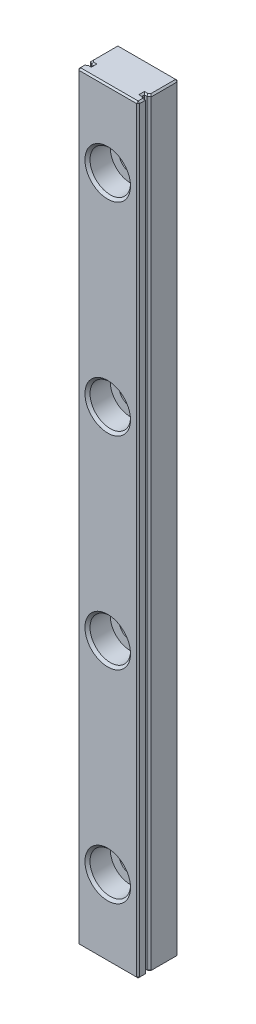
SolidWorks part; units mm, degrees
material "Простая углеродистая сталь"
ref_plane "Спереди" through (0, 0, 0) normal (0, 0, 1) x (1, 0, 0)
ref_plane "Сверху" through (0, 0, 0) normal (0, 1, 0) x (1, 0, 0)
ref_plane "Справа" through (0, 0, 0) normal (1, 0, 0) x (0, 0, -1)
sketch "Эскиз1" plane through (0, 0, 0) normal (0, 1, 0) x (1, 0, 0)
  line L0 (0, 0) -> (12, 0)
  line L1 (0, 0) -> (0, 8)
  line L2 (12, 0) -> (12, 8)
  line L3 (0, 8) -> (12, 8)
  dimension "D1" = 8
  dimension "D2" = 12
extrude "Бобышка-Вытянуть1" add sketch "Эскиз1" along normal blind 150
sketch "Эскиз2" plane through (0, 150, 0) normal (0, 1, 0) x (1, 0, 0)
  line L0 (12, 0) -> (12, 8) construction
  line L1 (11, 2.25) -> (11, 1.75)
  line L2 (11, 2.25) -> (11.5, 2.25)
  line L3 (11, 1.75) -> (11.5, 1.75)
  line L4 (12, 2.25) -> (12, 1.75) construction
  line L5 (11, 2) -> (12, 2) construction
  line L6 (0, 0) -> (12, 0) construction
  line L7 (12, 2) -> (11, 2) construction
  line L8 (11.5, 2.25) -> (11.5, 1.75) construction
  line L9 (12, 2.559) -> (12, 1.441)
  arc A0 (12, 2.559) -> (11.5, 2.25) centre (12, 2) ccw
  arc A1 (11.5, 1.75) -> (12, 1.441) centre (12, 2) ccw
  dimension "D4" = 0.5
  dimension "D1" = 0.5
  dimension "D2" = 1
  dimension "D3" = 2
extrude "Вырез-Вытянуть1" cut sketch "Эскиз2" against normal through all
sketch "Эскиз3" plane through (0, 150, 0) normal (0, 1, 0) x (1, 0, 0)
  line L0 (6, 0) -> (6, 8) construction
  line L1 (0, 0) -> (12, 0) construction
  line L2 (12, 8) -> (0, 8) construction
  line L3 (6, 4) -> (12, 4) construction
  line L4 (12, 2.559) -> (12, 8) construction
ref_plane "A" through (6, 0, 0) normal (1, 0, 0) x (0, 0, -1)
ref_plane "B" through (0, 0, -4) normal (0, 0, 1) x (1, 0, 0)
mirror "Зеркальное отражение1" about plane through (6, 0, 0) normal (1, 0, 0) of "Вырез-Вытянуть1"
sketch "Эскиз4" plane through (6, 0, 0) normal (1, 0, 0) x (0, 0, -1)
  line L0 (8, 135) -> (-11.3986, 135) construction
  line L1 (8, 150) -> (2.559, 150) construction
  line L2 (8, 150) -> (0, 150) construction
  line L3 (0, 150) -> (0, 133.1034) construction
  line L4 (0, 139) -> (4.5, 139)
  line L5 (4.5, 139) -> (4.5, 137.25)
  line L6 (4.5, 137.25) -> (8, 137.25)
  line L7 (8, 150) -> (8, 0) construction
  line L8 (8, 150) -> (8, 0) construction
  line L9 (0, 139) -> (0, 135)
  line L10 (8, 137.25) -> (8, 135)
  line L11 (0, 135) -> (8, 135)
  dimension "D1" = 15
  dimension "D2" = 4
  dimension "D3" = 4.5
  dimension "D4" = 2.25
revolve "Вырез-Повернуть1" cut sketch "Эскиз4" angle 360 about L0
chamfer "Фаска1" distance 0.5 angle 45 2 edges at (3.75, 135, -8) (2, 135, 0)
pattern_linear "Линейный массив1" count 4 spacing 40 along (0, -1, 0) of "Вырез-Повернуть1", "Фаска1"
chamfer "Фаска2" distance 0.3 angle 45 36 edges at (0.75, 150, -1.75) (1, 150, -2) (0.75, 150, -2.25) (0.2939, 150, -2.4755) (0, 150, -5.2795) (6, 150, -8) (12, 150, -5.2795) (11.7061, 150, -2.4755) (11.25, 150, -2.25) (11, 150, -2) (11.25, 150, -1.75) (11.7061, 150, -1.5245) (12, 150, -0.7205) (6, 150, 0) (0.2939, 150, -1.5245) (0, 150, -0.7205) (6, 0, 0) (12, 75, 0) (12, 0, -0.7205) (11.7061, 0, -1.5245) (11.25, 0, -1.75) (11, 0, -2) (11.25, 0, -2.25) (11.7061, 0, -2.4755) (12, 0, -5.2795) (12, 75, -8) (6, 0, -8) (0, 75, -8) (0, 0, -5.2795) (0.2939, 0, -2.4755) (0.75, 0, -2.25) (1, 0, -2) (0.75, 0, -1.75) (0.2939, 0, -1.5245) (0, 0, -0.7205) (0, 75, 0)
